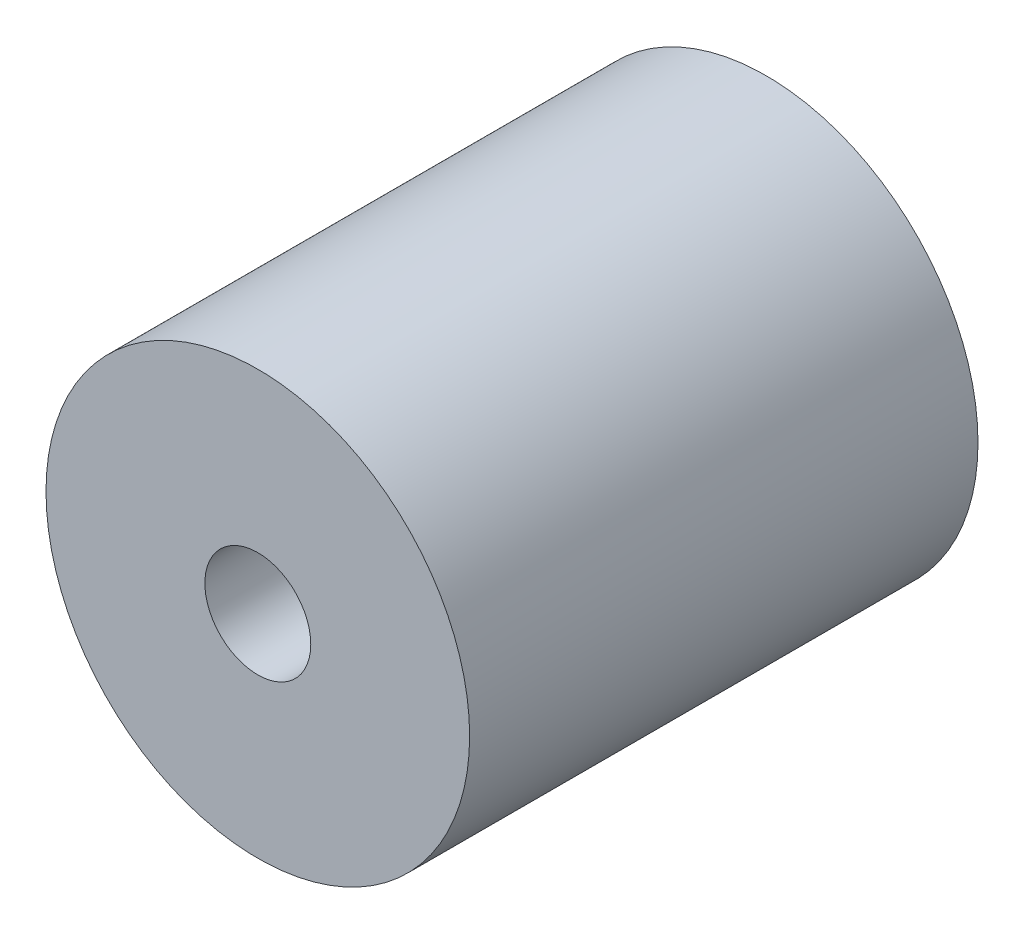
SolidWorks part; units mm, degrees
ref_plane "前视基准面" through (0, 0, 0) normal (0, 0, 1) x (1, 0, 0)
ref_plane "上视基准面" through (0, 0, 0) normal (0, 1, 0) x (1, 0, 0)
ref_plane "右视基准面" through (0, 0, 0) normal (1, 0, 0) x (0, 0, -1)
sketch "草图1" plane through (0, 0, 0) normal (0, 0, 1) x (1, 0, 0)
  circle A0 centre (0, 0) radius 10
  dimension "D1" = 20
extrude "凸台-拉伸1" add sketch "草图1" along normal blind 24
sketch "草图2" plane through (0, 0, 24) normal (0, 0, 1) x (1, 0, 0)
  circle A0 centre (0, 0) radius 2.5
  dimension "D1" = 5
extrude "切除-拉伸1" cut sketch "草图2" against normal blind 12
sketch "草图3" plane through (0, 0, 0) normal (0, 0, -1) x (-1, 0, 0)
  circle A0 centre (0, 0) radius 4
  dimension "D1" = 8
extrude "切除-拉伸2" cut sketch "草图3" against normal blind 12
